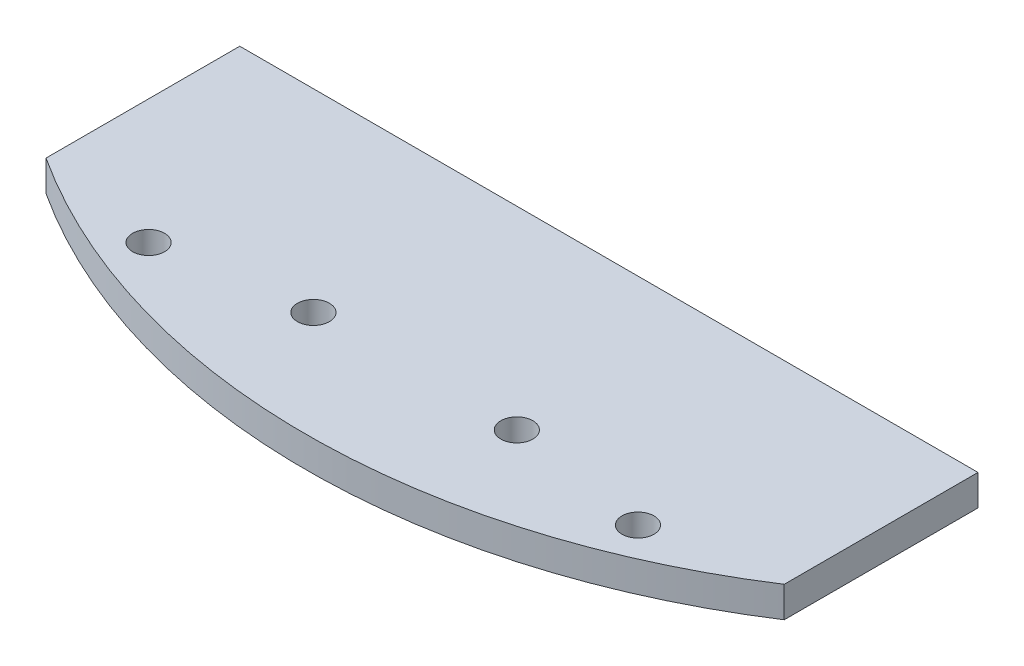
SolidWorks part; units mm, degrees
ref_plane "Front Plane" through (0, 0, 0) normal (0, 0, 1) x (1, 0, 0)
ref_plane "Top Plane" through (0, 0, 0) normal (0, 1, 0) x (1, 0, 0)
ref_plane "Right Plane" through (0, 0, 0) normal (1, 0, 0) x (0, 0, -1)
sketch "Base w/ Motor Mounts" plane through (0, 0, 0) normal (0, 1, 0) x (1, 0, 0)
  line L0 (0, 70) -> (0, -70) construction
  line L1 (0, 0) -> (70, 0) construction
  circle A0 centre (0, 0) radius 70
  dimension "D6" = 140
sketch "Standoffs (top / bottom)" plane through (0, 0, 0) normal (0, 1, 0) x (1, 0, 0)
  line L0 (0, 0) -> (64.6716, 26.7878) construction
  line L1 (0, 0) -> (49.4975, 49.4975) construction
  line L2 (0, 0) -> (26.7878, 64.6716) construction
  line L3 (0, 0) -> (70, 0) construction
  line L4 (-70, 0) -> (70, 0) construction
  line L5 (0, 0) -> (64.6716, -26.7878) construction
  line L6 (0, 0) -> (49.4975, -49.4975) construction
  line L7 (0, 0) -> (26.7878, -64.6716) construction
  line L8 (0, 70) -> (0, -70) construction
  line L9 (0, 0) -> (-26.7878, -64.6716) construction
  line L10 (0, 0) -> (-49.4975, -49.4975) construction
  line L11 (0, 0) -> (-64.6716, -26.7878) construction
  line L12 (0, 0) -> (-26.7878, 64.6716) construction
  line L13 (0, 0) -> (-49.4975, 49.4975) construction
  line L14 (0, 0) -> (-64.6716, 26.7878) construction
  line L15 (25.2571, 60.976) -> (25.2571, 25.2571) construction
  circle A0 centre (0, 0) radius 70 construction
  circle A1 centre (25.2571, 60.976) radius 1.65
  circle A3 centre (60.976, 25.2571) radius 1.65
  circle A6 centre (60.976, -25.2571) radius 1.65
  circle A7 centre (25.2571, -60.976) radius 1.65
  circle A8 centre (-25.2571, -60.976) radius 1.65
  circle A9 centre (-60.976, -25.2571) radius 1.65
  circle A12 centre (-60.976, 25.2571) radius 1.65
  circle A13 centre (-25.2571, 60.976) radius 1.65
  dimension "D4" = 3.3
  dimension "D1" = 22.5
  dimension "D2" = 22.5
  dimension "D3" = 22.5
  dimension "D5" = 4
  dimension "D7" = 4
  dimension "D6" = 35.7189
sketch "Pi and Mega Standoffs" plane through (0, 0, 0) normal (0, 1, 0) x (1, 0, 0)
  line L0 (0, 70) -> (0, -70) construction
  line L1 (-38.1, 55) -> (19.9, 55) construction
  line L2 (-38.1, 55) -> (-38.1, 6) construction
  line L3 (-38.1, 6) -> (19.9, 6) construction
  line L4 (19.9, 55) -> (19.9, 6) construction
  line L5 (-38.1, 55) -> (19.9, 6) construction
  line L6 (-38.1, 6) -> (19.9, 55) construction
  line L7 (0, 0) -> (70, 0) construction
  line L8 (-38.1, -6) -> (38.1, -6) construction
  line L9 (-38.1, -6) -> (-38.1, -54.2) construction
  line L10 (-38.1, -54.2) -> (38.1, -54.2) construction
  line L11 (38.1, -6) -> (38.1, -54.2) construction
  line L12 (-38.1, -6) -> (38.1, -54.2) construction
  line L13 (-38.1, -54.2) -> (38.1, -6) construction
  circle A0 centre (-38.1, 55) radius 1.4
  circle A1 centre (19.9, 55) radius 1.4
  circle A2 centre (19.9, 6) radius 1.4
  circle A3 centre (-38.1, 6) radius 1.4
  circle A4 centre (-38.1, -54.2) radius 1.65
  circle A5 centre (-36.8, -6) radius 1.65
  circle A6 centre (38.1, -6) radius 1.65
  point P0 (-10.6204, 31.3097)
  point P11 (0, -30.1)
  dimension "D3" = 2.8
  dimension "D5" = 3.3
  dimension "D1" = 49
  dimension "D2" = 58
  dimension "D4" = 76.2
  dimension "D6" = 1.3
  dimension "D7" = 74.9
  dimension "D8" = 48.2
  dimension "D9" = 6
  dimension "D10" = 6
sketch "Sketch2" plane through (0, 0, 0) normal (0, 1, 0) x (1, 0, 0)
  line L0 (-38.1, -38.723) -> (-38.1, -58.723)
  line L1 (-38.1, -6) -> (-38.1, -54.2) construction
  line L2 (-38.1, -38.723) -> (38.1, -38.723)
  line L3 (38.1, -6) -> (38.1, -54.2) construction
  line L4 (38.1, -38.723) -> (38.1, -58.723)
  line L5 (0, -58.723) -> (10.5, -58.723)
  line L6 (0, 70) -> (0, -70) construction
  line L7 (0, -58.723) -> (-10.5, -58.723)
  circle A0 centre (0, 0) radius 70 construction
  arc A1 (38.1, -58.723) -> (-38.1, -58.723) centre (0, 0) cw
  circle A2 centre (-25.2571, -60.976) radius 1.65
  circle A3 centre (25.2571, -60.976) radius 1.65
  circle A4 centre (10.5, -58.723) radius 1.65
  circle A5 centre (-10.5, -58.723) radius 1.65
  dimension "D1" = 3.3
  dimension "D3" = 3.3
  dimension "D2" = 10.5
extrude "Boss-Extrude2" add sketch "Sketch2" along normal blind 3.175 contours A1 L4 L2 L0 A3 A2
equation "\"D7@Standoffs (top / bottom)\" = \"D5@Standoffs (top / bottom)\""
equation "\"D10@Pi and Mega Standoffs\"=\"D9@Pi and Mega Standoffs\""
